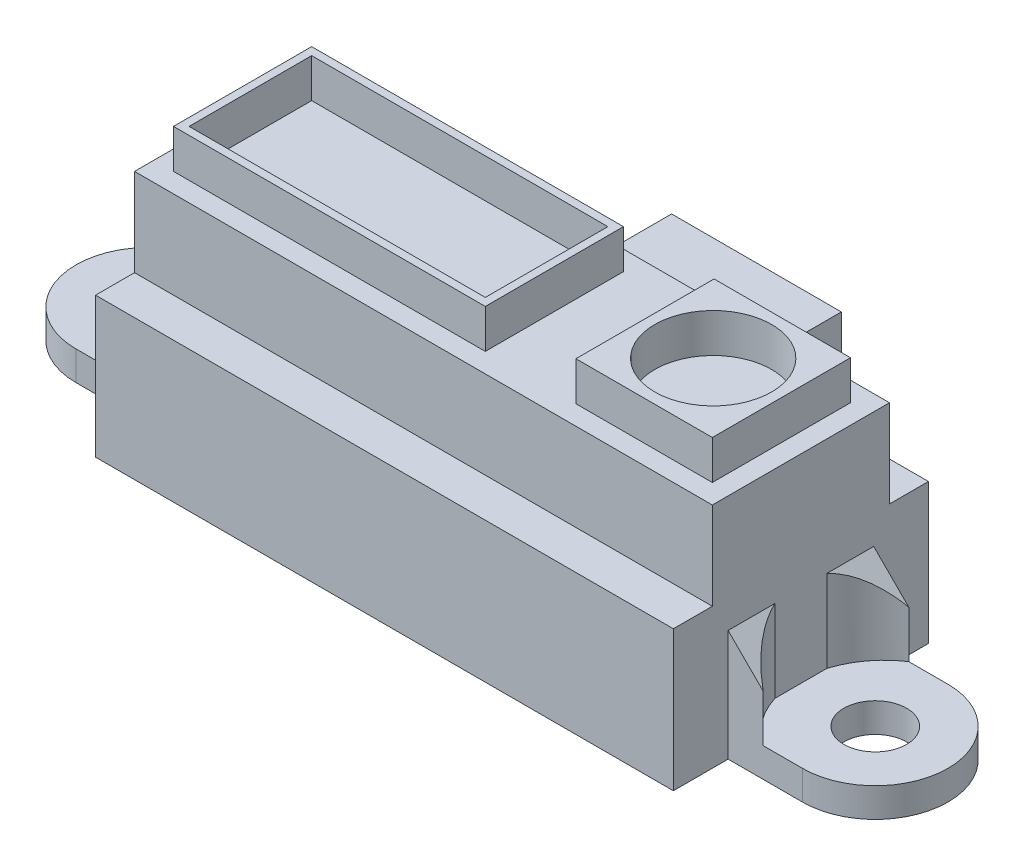
SolidWorks part; units mm, degrees
material "ABS"
ref_plane "Front Plane" through (0, 0, 0) normal (0, 0, 1) x (1, 0, 0)
ref_plane "Top Plane" through (0, 0, 0) normal (0, 1, 0) x (1, 0, 0)
ref_plane "Right Plane" through (0, 0, 0) normal (1, 0, 0) x (0, 0, -1)
sketch "Sketch1" plane through (0, 0, 0) normal (0, 1, 0) x (1, 0, 0)
  line L0 (-14.055, 5.775) -> (-5.355, 5.775)
  line L1 (-14.825, -6.545) -> (14.825, -6.545)
  line L2 (-14.825, -6.545) -> (-14.825, 6.545)
  line L3 (-14.825, 6.545) -> (-5.355, 6.545)
  line L4 (14.825, -6.545) -> (14.825, 6.545)
  line L5 (-14.825, -6.545) -> (14.825, 6.545) construction
  line L6 (-14.825, 6.545) -> (14.825, -6.545) construction
  line L7 (14.055, -5.775) -> (14.055, 5.775)
  line L8 (-14.055, -5.775) -> (14.055, -5.775)
  line L9 (-14.055, -5.775) -> (-14.055, 5.775)
  line L10 (0, 13.6604) -> (0, -14.8955) construction
  line L11 (-5.355, 6.545) -> (-5.355, 5.775)
  line L12 (5.355, 6.545) -> (5.355, 5.775)
  line L13 (5.355, 6.545) -> (14.825, 6.545)
  line L14 (-14.825, 6.545) -> (14.825, 6.545) construction
  line L15 (5.355, 5.775) -> (14.055, 5.775)
  line L16 (-14.055, 5.775) -> (14.055, 5.775) construction
  point P0 (0, 0)
  dimension "D1" = 29.65
  dimension "D2" = 13.09
  dimension "D3" = 0.77
  dimension "D4" = 5.355
extrude "Boss-Extrude1" add sketch "Sketch1" along normal blind 7.2
sketch "Sketch2" plane through (0, 0, 0) normal (0, 1, 0) x (1, 0, 0)
  line L0 (0, 11.5372) -> (0, -12.4354) construction
  line L1 (18.64, 3.735) -> (14.825, 3.735)
  line L2 (14.825, -6.545) -> (14.825, 6.545) construction
  line L3 (18.64, -3.735) -> (14.825, -3.735)
  line L4 (31.1664, 0) -> (-32.4313, 0) construction
  line L5 (14.825, 3.735) -> (14.825, -3.735)
  line L6 (-14.825, 3.735) -> (-14.825, -3.735)
  line L7 (-18.64, -3.735) -> (-14.825, -3.735)
  line L8 (-18.64, 3.735) -> (-14.825, 3.735)
  circle A0 centre (18.64, 0) radius 1.61
  arc A1 (18.64, -3.735) -> (18.64, 3.735) centre (18.64, 0) ccw
  arc A2 (-18.64, -3.735) -> (-18.64, 3.735) centre (-18.64, 0) cw
  circle A3 centre (-18.64, 0) radius 1.61
  point P12 (22.375, 0)
  point P20 (-22.375, 0)
  dimension "D1" = 3.22
  dimension "D2" = 7.47
  dimension "D3" = 7.55
extrude "Boss-Extrude2" add sketch "Sketch2" along normal blind 1.5
sketch "Sketch3" plane through (0, 7.2, 0) normal (0, 1, 0) x (1, 0, 0)
  line L1 (-14.825, -6.545) -> (14.825, -6.545)
  line L2 (-14.825, -6.545) -> (-14.825, 6.545)
  line L3 (-14.825, 6.545) -> (-5.355, 6.545)
  line L4 (14.825, -6.545) -> (14.825, 6.545)
  line L6 (-5.355, 5.775) -> (-5.355, 6.545) construction
  line L7 (-5.355, 6.545) -> (-5.355, 4.325)
  line L8 (-5.355, 4.325) -> (5.355, 4.325)
  line L9 (5.355, 6.545) -> (14.825, 6.545)
  line L10 (5.355, 4.325) -> (5.355, 6.545)
  dimension "D1" = 2.22
extrude "Boss-Extrude3" add sketch "Sketch3" against normal blind 0.7
ref_plane "Plane1" through (0, 3.37, 0) normal (0, 1, 0) x (1, 0, 0)
sketch "Sketch7" plane through (0, 1.5, 0) normal (0, 1, 0) x (1, 0, 0)
  line L0 (-14.825, 3.735) -> (-16.625, 3.735)
  line L1 (-14.825, 3.735) -> (-18.64, 3.735) construction
  line L2 (-14.825, 3.735) -> (-14.825, 1.335)
  line L3 (-14.825, -3.735) -> (-14.825, 3.735) construction
  line L4 (-31.4685, 0) -> (3.2483, 0) construction
  line L5 (-14.825, -3.735) -> (-14.825, -1.335)
  line L6 (-14.825, -3.735) -> (-16.625, -3.735)
  line L7 (0, 19.5434) -> (0, -19.1533) construction
  line L8 (14.825, -3.735) -> (16.625, -3.735)
  line L9 (14.825, -3.735) -> (14.825, -1.335)
  line L10 (14.825, 3.735) -> (14.825, 1.335)
  line L11 (14.825, 3.735) -> (16.625, 3.735)
  arc A0 (-14.825, 1.335) -> (-16.625, 3.735) centre (-19.105, 0) ccw
  arc A1 (-14.825, -1.335) -> (-16.625, -3.735) centre (-19.105, 0) cw
  arc A2 (14.825, -1.335) -> (16.625, -3.735) centre (19.105, 0) ccw
  arc A3 (14.825, 1.335) -> (16.625, 3.735) centre (19.105, 0) cw
  dimension "D1" = 1.8
  dimension "D2" = 2.4
extrude "Boss-Extrude7" add sketch "Sketch7" along normal blind 4.22
sketch "Sketch8" plane through (0, 0, 0) normal (0, 0, 1) x (1, 0, 0)
  line L0 (-14.825, 5.72) -> (-16.625, 3.92)
  line L1 (-16.625, 5.72) -> (-16.625, 1.5) construction
  line L2 (0, 34.8249) -> (0, -17.4317) construction
  line L3 (14.825, 5.72) -> (16.625, 3.92)
  line L4 (-16.625, 5.72) -> (-14.825, 5.72) construction
  line L5 (-16.625, 3.92) -> (-16.625, 5.72)
  line L6 (-16.625, 5.72) -> (-14.825, 5.72)
  line L7 (16.625, 3.92) -> (16.625, 5.72)
  line L8 (16.625, 5.72) -> (14.825, 5.72)
  dimension "D1" = 45
extrude "Cut-Extrude1" cut sketch "Sketch8" against normal through all and the other way through all
sketch "Esquisse1" plane through (0, 7.2, 0) normal (0, 1, 0) x (1, 0, 0)
  line L0 (-14.825, 6.545) -> (-14.825, -6.545) construction
  line L1 (-14.825, 4.545) -> (14.825, 4.545)
  line L2 (-14.825, 4.545) -> (-14.825, -4.545)
  line L3 (-14.825, -4.545) -> (14.825, -4.545)
  line L4 (14.825, 4.545) -> (14.825, -4.545)
  line L5 (14.825, -6.545) -> (14.825, 6.545) construction
  line L6 (-5.355, 6.545) -> (-14.825, 6.545) construction
  line L7 (-14.825, -6.545) -> (14.825, -6.545) construction
  dimension "D1" = 2
  dimension "D2" = 2
extrude "Boss.-Extru.1" add sketch "Esquisse1" along normal blind 4.5
sketch "Esquisse3" plane through (0, 11.7, 0) normal (0, 1, 0) x (1, 0, 0)
  line L0 (14.825, 4.545) -> (5.355, 4.545) construction
  line L1 (-13.825, 3.545) -> (2.175, 3.545)
  line L2 (-13.825, 3.545) -> (-13.825, -3.545)
  line L3 (-13.825, -3.545) -> (2.175, -3.545)
  line L4 (2.175, 3.545) -> (2.175, -3.545)
  line L5 (6.825, 3.545) -> (13.825, 3.545)
  line L6 (6.825, 3.545) -> (6.825, -3.545)
  line L7 (6.825, -3.545) -> (13.825, -3.545)
  line L8 (13.825, 3.545) -> (13.825, -3.545)
  line L9 (14.825, -4.545) -> (14.825, 4.545) construction
  line L10 (-5.355, 4.545) -> (-14.825, 4.545) construction
  line L11 (-14.825, 4.545) -> (-14.825, -4.545) construction
  line L12 (-14.825, -4.545) -> (14.825, -4.545) construction
  dimension "D1" = 16
  dimension "D2" = 7
  dimension "D3" = 1
  dimension "D4" = 1
  dimension "D5" = 1
  dimension "D6" = 1
  dimension "D7" = 1
  dimension "D8" = 1
extrude "Boss.-Extru.2" add sketch "Esquisse3" along normal blind 2
sketch "Esquisse4" plane through (0, 13.7, 0) normal (0, 1, 0) x (1, 0, 0)
  line L0 (2.175, 3.545) -> (-13.825, 3.545) construction
  line L1 (-13.425, 3.145) -> (1.775, 3.145)
  line L2 (-13.425, 3.145) -> (-13.425, -3.145)
  line L3 (-13.425, -3.145) -> (1.775, -3.145)
  line L4 (1.775, 3.145) -> (1.775, -3.145)
  line L5 (-13.825, 3.545) -> (-13.825, -3.545) construction
  line L6 (-13.825, -3.545) -> (2.175, -3.545) construction
  line L7 (2.175, -3.545) -> (2.175, 3.545) construction
  line L8 (13.825, -3.545) -> (13.825, 3.545) construction
  line L9 (13.825, 3.545) -> (6.825, 3.545) construction
  circle A0 centre (10.325, 0) radius 3
  dimension "D5" = 3.5
  dimension "D7" = 6
  dimension "D1" = 0.4
  dimension "D2" = 0.4
  dimension "D3" = 0.4
  dimension "D4" = 0.4
  dimension "D6" = 3.545
extrude "Enlèv. mat.-Extru.1" cut sketch "Esquisse4" against normal blind 2
sketch "Esquisse5" plane through (0, 6.5, 0) normal (0, -1, 0) x (1, 0, 0)
  line L0 (5.355, -4.545) -> (-5.355, -4.545) construction
  line L1 (-4.355, -3.545) -> (4.355, -3.545)
  line L2 (-4.355, -3.545) -> (-4.355, -4.545)
  line L3 (-4.355, -4.545) -> (4.355, -4.545)
  line L4 (4.355, -3.545) -> (4.355, -4.545)
  line L5 (-5.355, -4.325) -> (-5.355, -5.775) construction
  line L6 (5.355, -5.775) -> (5.355, -4.325) construction
  dimension "D1" = 1
  dimension "D2" = 1
  dimension "D3" = 1
extrude "Boss.-Extru.3" add sketch "Esquisse5" along normal blind 8
sketch "Esquisse6" plane through (0, 0, -4.545) normal (0, 0, -1) x (-1, 0, 0)
  line L0 (4.355, -1.5) -> (-4.355, -1.5) construction
  line L1 (-4.355, -1.5) -> (-3.355, -1.5)
  line L2 (-4.355, -1.5) -> (-4.355, 6.5)
  line L3 (-4.355, 6.5) -> (4.355, 6.5)
  line L4 (4.355, -1.5) -> (4.355, 6.5)
  line L5 (3.355, -1.5) -> (4.355, -1.5)
  line L6 (-3.355, -1.5) -> (-3.355, 5.5)
  line L7 (-3.355, 5.5) -> (3.355, 5.5)
  line L8 (3.355, -1.5) -> (3.355, 5.5)
  dimension "D1" = 1
  dimension "D2" = 1
  dimension "D4" = 1
extrude "Boss.-Extru.4" add sketch "Esquisse6" along normal blind 8
